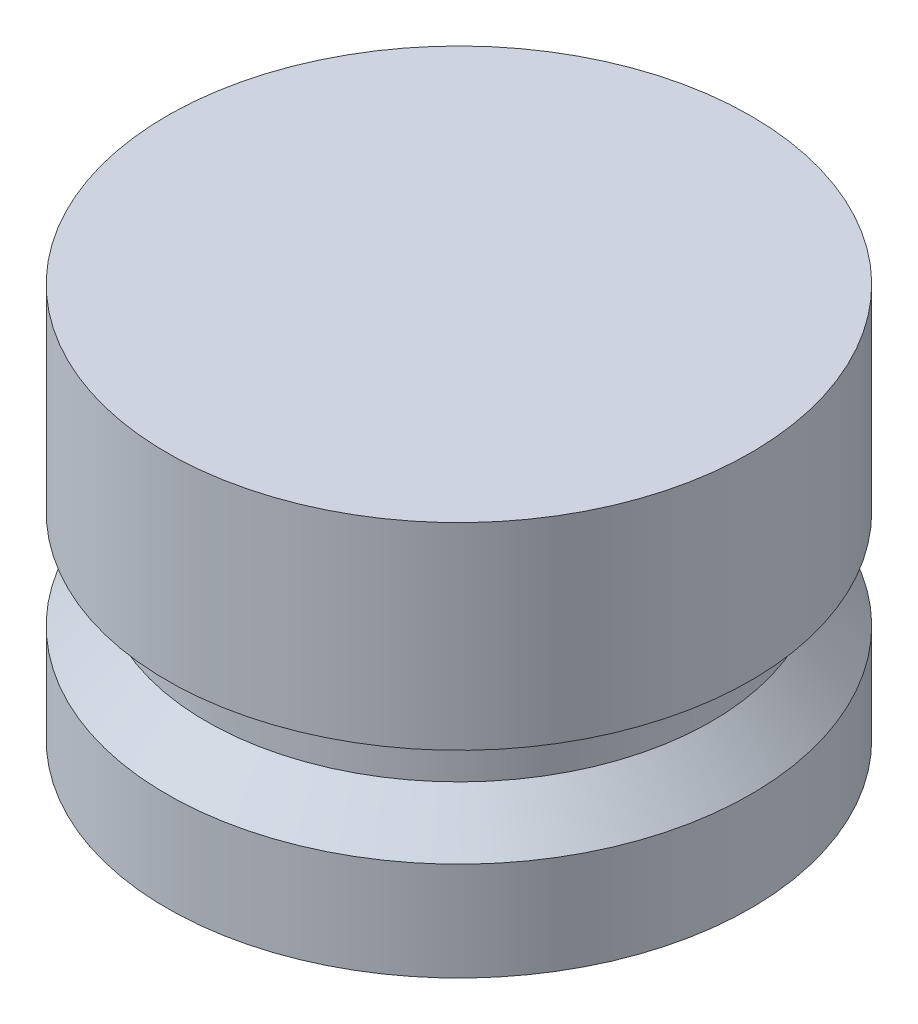
SolidWorks part; units mm, degrees
ref_plane "Front Plane" through (0, 0, 0) normal (0, 0, 1) x (1, 0, 0)
ref_plane "Top Plane" through (0, 0, 0) normal (0, 1, 0) x (1, 0, 0)
ref_plane "Right Plane" through (0, 0, 0) normal (1, 0, 0) x (0, 0, -1)
sketch "Sketch1" plane through (0, 0, 0) normal (0, 0, 1) x (1, 0, 0)
  line L0 (0, 0) -> (0, 12.7) construction
  line L1 (0, 0) -> (-9.398, 0)
  line L2 (-9.398, 0) -> (-9.398, 3.175)
  line L4 (-8.128, 4.572) -> (-8.128, 6.35)
  line L5 (-8.128, 6.35) -> (-9.398, 6.35)
  line L6 (-9.398, 6.35) -> (-9.398, 12.7)
  line L7 (-9.398, 12.7) -> (0, 12.7)
  line L8 (-9.525, 16.6801) -> (-9.525, -9.6051) construction
  line L9 (0, 0) -> (0, 12.7)
  line L10 (-8.128, 4.572) -> (-9.398, 3.175)
  dimension "D1" = 12.7
  dimension "D2" = 9.398
  dimension "D3" = 1.778
  dimension "D4" = 3.175
  dimension "D5" = 9.525
  dimension "D6" = 8.128
  dimension "D7" = 6.35
revolve "Revolve1" add sketch "Sketch1" angle 360 about L9
